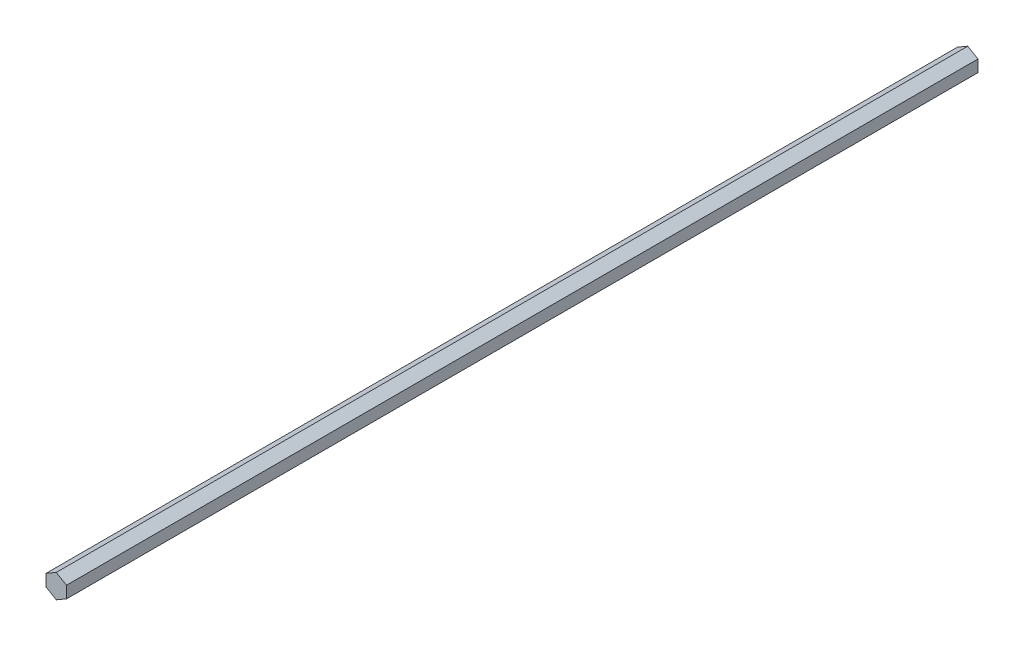
SolidWorks part; units mm, degrees
material "6061 Alloy"
ref_plane "Front Plane" through (0, 0, 0) normal (0, 0, 1) x (1, 0, 0)
ref_plane "Top Plane" through (0, 0, 0) normal (0, 1, 0) x (1, 0, 0)
ref_plane "Right Plane" through (0, 0, 0) normal (1, 0, 0) x (0, 0, -1)
sketch "Sketch1" plane through (0, 0, 0) normal (0, 0, 1) x (1, 0, 0)
  line L0 (-6.35, 0) -> (6.35, 0) construction
  line L9 (0, 7.3323) -> (-6.35, 3.6662) construction
  line L10 (-6.35, 3.6662) -> (-6.35, -3.6662) construction
  line L11 (-6.35, -3.6662) -> (0, -7.3323) construction
  line L12 (0, -7.3323) -> (6.35, -3.6662) construction
  line L13 (6.35, -3.6662) -> (6.35, 3.6662) construction
  line L14 (6.35, 3.6662) -> (0, 7.3323) construction
  circle A3 centre (0, 0) radius 6.35 construction
  point P4 (0, 0)
  dimension "Width" = 12.7
sketch "Sketch2" plane through (0, 0, 0) normal (1, 0, 0) x (0, 0, -1)
  line L0 (281.94, 7.3323) -> (-281.94, 7.3323) construction
  point P3 (-267.335, 7.3323)
  point P4 (0, 7.3323)
  point P5 (267.335, 7.3323)
  dimension "Length" = 563.88
  dimension "D1" = 14.605
  dimension "D2" = 14.605
sketch "Sketch3" plane through (0, 0, 0) normal (0, 0, 1) x (1, 0, 0)
  line L1 (0, 7.3323) -> (6.35, 3.6662)
  line L2 (6.35, 3.6662) -> (6.35, -3.6662)
  line L3 (6.35, -3.6662) -> (0, -7.3323)
  line L4 (0, -7.3323) -> (-6.35, -3.6662)
  line L5 (-6.35, -3.6662) -> (-6.35, 3.6662)
  line L6 (-6.35, 3.6662) -> (0, 7.3323)
extrude "Boss-Extrude1" add sketch "Sketch3" along normal mid plane 563.88
equation "\"D1@Boss-Extrude1\" = \"Length@Sketch2\""
equation "\"D1@Sketch2\" = \"Width@Sketch1\" * 1.15"
equation "\"D2@Sketch2\"=\"D1@Sketch2\""
